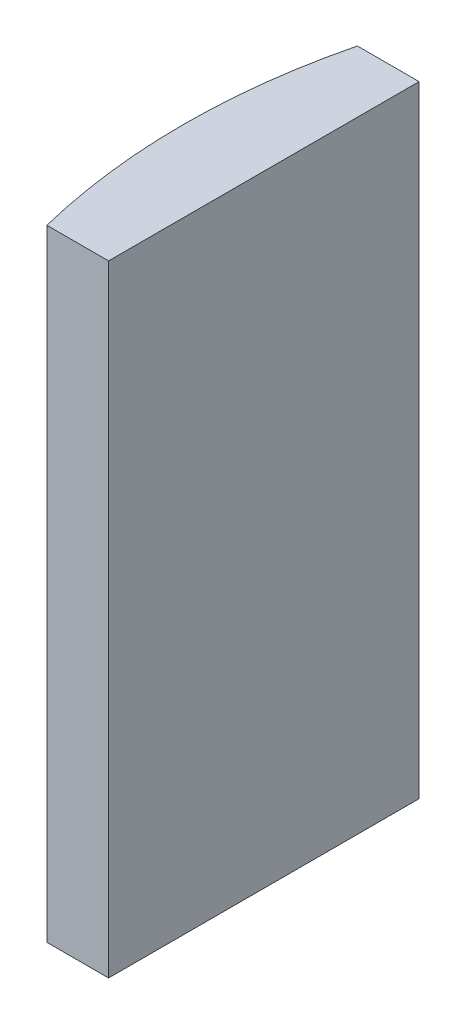
SolidWorks part; units mm, degrees
ref_plane "前视基准面" through (0, 0, 0) normal (0, 0, 1) x (1, 0, 0)
ref_plane "上视基准面" through (0, 0, 0) normal (0, 1, 0) x (1, 0, 0)
ref_plane "右视基准面" through (0, 0, 0) normal (1, 0, 0) x (0, 0, -1)
sketch "草图1" plane through (0, 0, 0) normal (0, 1, 0) x (1, 0, 0)
  line L0 (10.7432, 0) -> (-19.1624, 0) construction
  line L1 (-15.7112, 5) -> (-13.7248, 5)
  line L2 (-15.7112, -5) -> (-13.7248, -5)
  line L3 (-13.7248, 5) -> (-13.7248, -5)
  arc A0 (-15.7112, 5) -> (-15.7112, -5) centre (4.3552, 0) ccw
  point P19 (-16.3248, 0)
  point P20 (-13.7248, 0)
  dimension "D2" = 5
  dimension "D3" = 20.68
  dimension "D4" = 2.6
  dimension "D1" = 5
extrude "凸台-拉伸1" add sketch "草图1" along normal blind 20
